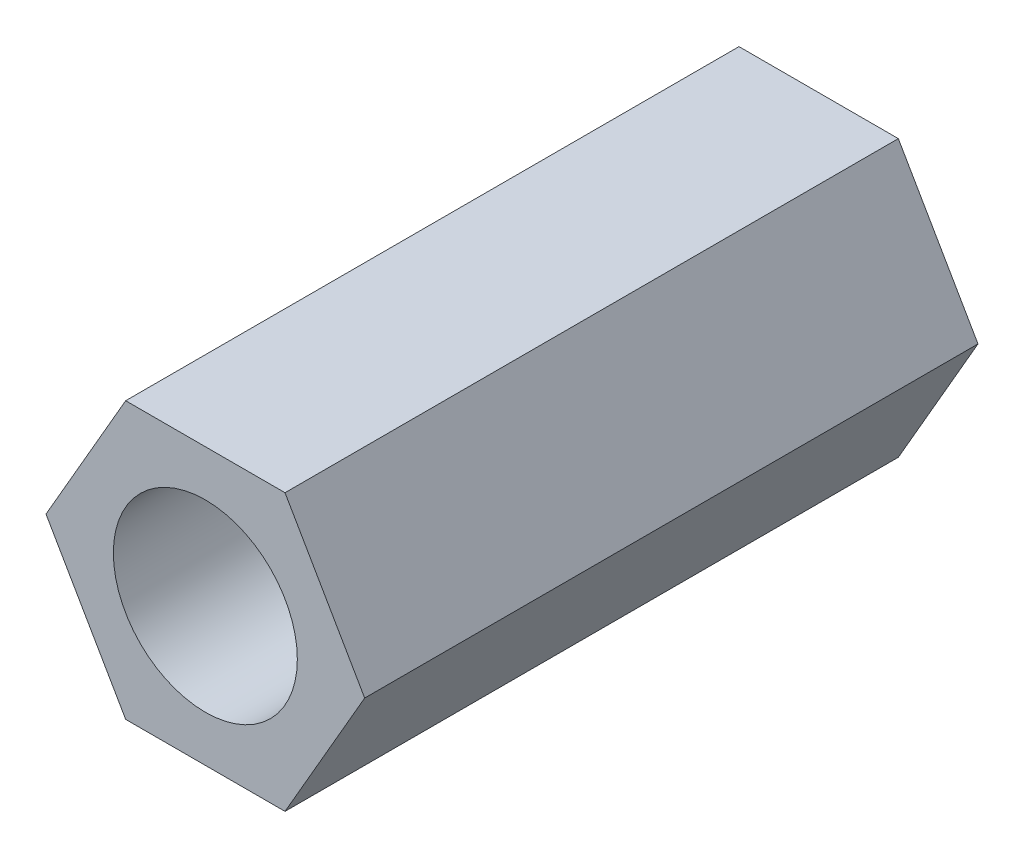
SolidWorks part; units mm, degrees
ref_plane "Plan de face" through (0, 0, 0) normal (0, 0, 1) x (1, 0, 0)
ref_plane "Plan de dessus" through (0, 0, 0) normal (0, 1, 0) x (1, 0, 0)
ref_plane "Plan de droite" through (0, 0, 0) normal (1, 0, 0) x (0, 0, -1)
sketch "Esquisse1" plane through (0, 0, 0) normal (0, 0, 1) x (1, 0, 0)
  line L1 (2.5981, 0) -> (1.299, 2.25)
  line L2 (1.299, 2.25) -> (-1.299, 2.25)
  line L3 (-1.299, 2.25) -> (-2.5981, 0)
  line L4 (-2.5981, 0) -> (-1.299, -2.25)
  line L5 (-1.299, -2.25) -> (1.299, -2.25)
  line L6 (1.299, -2.25) -> (2.5981, 0)
  circle A0 centre (0, 0) radius 2.25 construction
  circle A1 centre (0, 0) radius 1.5
  dimension "D1" = 4.5
  dimension "D2" = 3
extrude "Boss.-Extru.1" add sketch "Esquisse1" along normal blind 10
